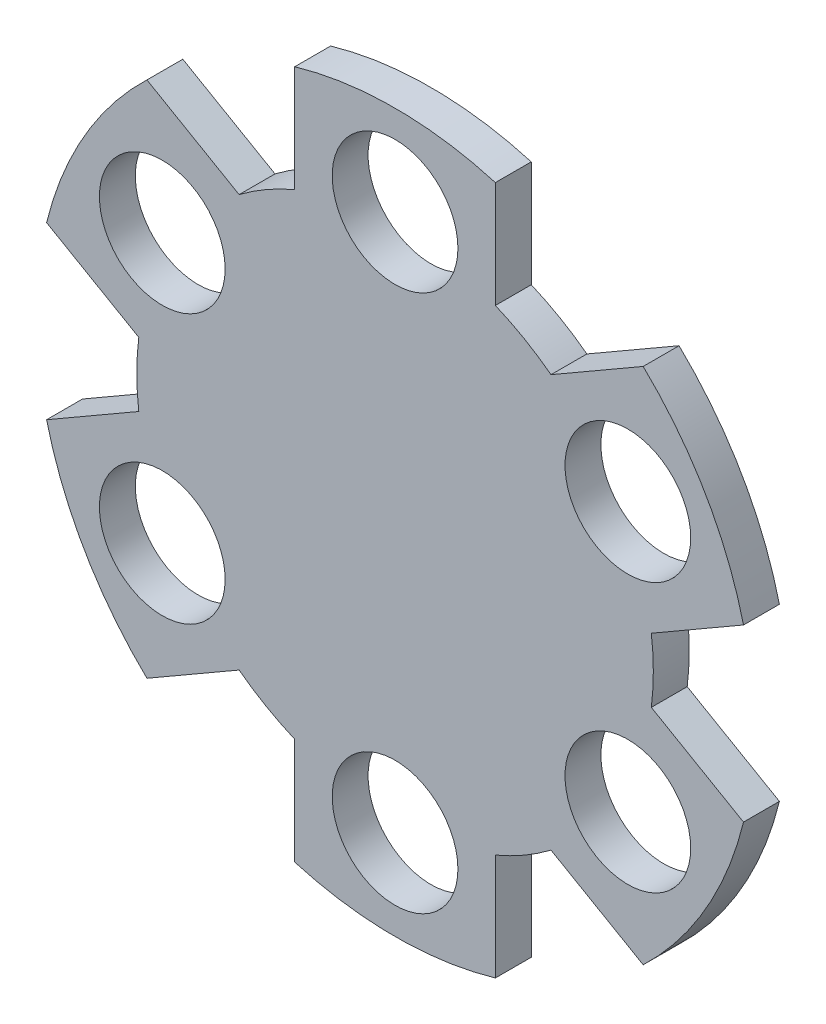
SolidWorks part; units mm, degrees
ref_plane "Front Plane" through (0, 0, 0) normal (0, 0, 1) x (1, 0, 0)
ref_plane "Top Plane" through (0, 0, 0) normal (0, 1, 0) x (1, 0, 0)
ref_plane "Right Plane" through (0, 0, 0) normal (1, 0, 0) x (0, 0, -1)
sketch "Sketch1" plane through (0, 0, 0) normal (0, 0, 1) x (1, 0, 0)
  line L0 (0, 0) -> (61.8183, 0) construction
  line L1 (-15.875, 15.875) -> (15.875, 15.875) construction
  line L2 (-15.875, 15.875) -> (-15.875, -15.875) construction
  line L3 (-15.875, -15.875) -> (15.875, -15.875) construction
  line L4 (15.875, 15.875) -> (15.875, -15.875) construction
  line L5 (0, 0) -> (0, 78.2171) construction
  line L6 (0, 0) -> (-20.6025, 11.8949) construction
  circle A0 centre (0, 0) radius 31.75
  circle A1 centre (0, 23.7897) radius 5.5626
  circle A2 centre (20.6025, 11.8949) radius 5.5626
  circle A3 centre (20.6025, -11.8949) radius 5.5626
  circle A4 centre (0, -23.7897) radius 5.5626
  circle A5 centre (-20.6025, -11.8949) radius 5.5626
  circle A6 centre (-20.6025, 11.8949) radius 5.5626
  circle A7 centre (0, 0) radius 23.7897 construction
  dimension "D1" = 31.75
  dimension "D5" = 11.1252
  dimension "D6" = 63.5
  dimension "D2" = 31.75
  dimension "D3" = 15.875
  dimension "D4" = 15.875
extrude "Extrude1" add sketch "Sketch1" along normal blind 3.175
sketch "Sketch2" plane through (0, 0, 0) normal (0, 0, -1) x (-1, 0, 0)
  line L0 (0, 0) -> (0, 33.6605) construction
  line L1 (0, 0) -> (39.8265, 0) construction
  line L2 (8.8788, 21.0617) -> (8.8788, 30.4833)
  line L6 (-8.8788, 30.4833) -> (-8.8788, 21.0617)
  line L8 (22.6794, 2.8416) -> (30.8387, 7.5524)
  line L10 (13.8006, 18.2201) -> (21.9599, 22.9309)
  line L12 (13.8006, -18.2201) -> (21.9599, -22.9309)
  line L14 (22.6794, -2.8416) -> (30.8387, -7.5524)
  line L16 (-8.8788, -21.0617) -> (-8.8788, -30.4833)
  line L17 (8.8788, -21.0617) -> (8.8788, -30.4833)
  line L18 (-22.6794, -2.8416) -> (-30.8387, -7.5524)
  line L19 (-13.8006, -18.2201) -> (-21.9599, -22.9309)
  line L20 (-13.8006, 18.2201) -> (-21.9599, 22.9309)
  line L21 (-22.6794, 2.8416) -> (-30.8387, 7.5524)
  line L38 (-8.8788, 21.0617) -> (-8.8788, 30.4833) [skipped]
  circle A0 centre (0, 0) radius 22.8567 construction
  circle A1 centre (0, 0) radius 31.75 construction
  arc A3 (8.8788, 21.0617) -> (13.8006, 18.2201) centre (0, 0) cw
  arc A4 (8.8788, 30.4833) -> (21.9599, 22.9309) centre (0, 0) cw
  arc A5 (22.6794, 2.8416) -> (22.6794, -2.8416) centre (0, 0) cw
  arc A6 (30.8387, 7.5524) -> (30.8387, -7.5524) centre (0, 0) cw
  arc A7 (13.8006, -18.2201) -> (8.8788, -21.0617) centre (0, 0) cw
  arc A8 (21.9599, -22.9309) -> (8.8788, -30.4833) centre (0, 0) cw
  arc A9 (-8.8788, -21.0617) -> (-13.8006, -18.2201) centre (0, 0) cw
  arc A10 (-8.8788, -30.4833) -> (-21.9599, -22.9309) centre (0, 0) cw
  arc A11 (-22.6794, -2.8416) -> (-22.6794, 2.8416) centre (0, 0) cw
  arc A12 (-30.8387, -7.5524) -> (-30.8387, 7.5524) centre (0, 0) cw
  arc A13 (-13.8006, 18.2201) -> (-8.8788, 21.0617) centre (0, 0) cw
  arc A14 (-21.9599, 22.9309) -> (-8.8788, 30.4833) centre (0, 0) cw
extrude "Cut-Extrude1" cut sketch "Sketch2" against normal through all
equation "\"D3@Sketch1\" = \"D1@Sketch1\" / 2"
equation "\"D4@Sketch1\"=\"D2@Sketch1\" / 2"
